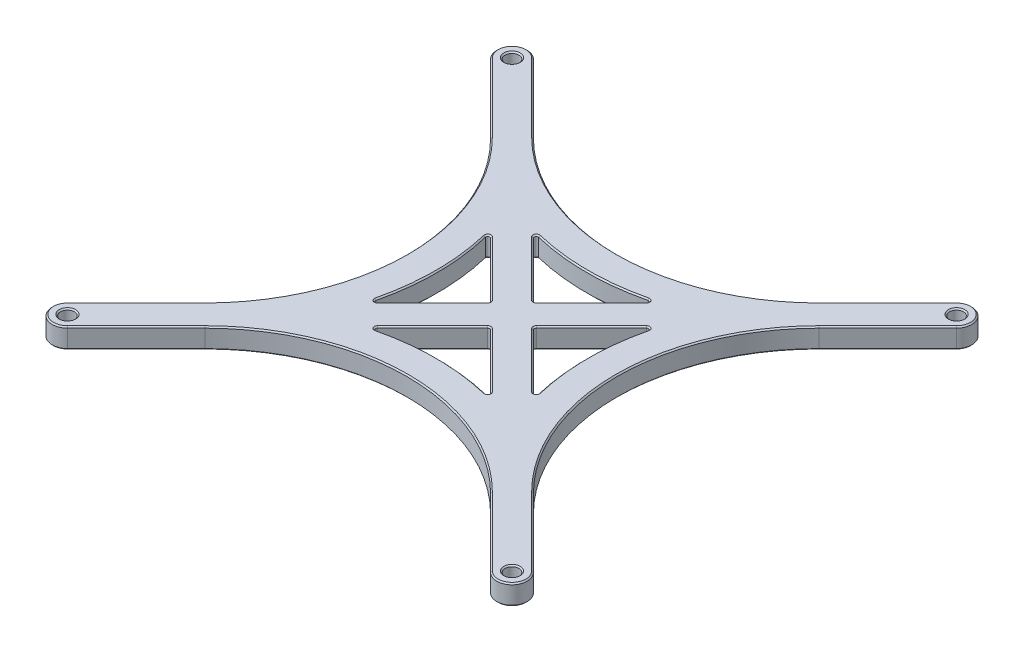
SolidWorks part; units mm, degrees
ref_plane "Front Plane" through (0, 0, 0) normal (0, 0, 1) x (1, 0, 0)
ref_plane "Top Plane" through (0, 0, 0) normal (0, 1, 0) x (1, 0, 0)
ref_plane "Right Plane" through (0, 0, 0) normal (1, 0, 0) x (0, 0, -1)
sketch "Sketch1" plane through (0, 0, 0) normal (0, 1, 0) x (1, 0, 0)
  line L0 (45.3593, 52.0945) -> (62.6658, 69.401)
  line L3 (-3.3676, 3.3676) -> (18.2135, 24.9487)
  line L18 (3.3676, -3.3676) -> (24.9487, 18.2135)
  line L19 (94.3407, 87.6055) -> (77.0342, 70.299)
  line L20 (3.3676, 143.0676) -> (24.9487, 121.4865)
  line L21 (-3.3676, 136.3324) -> (18.2135, 114.7513)
  line L22 (121.4865, 24.9487) -> (143.0676, 3.3676)
  line L23 (121.4865, 114.7513) -> (143.0676, 136.3324)
  line L24 (87.6055, 45.3593) -> (70.299, 62.6658)
  line L25 (52.0945, 94.3407) -> (69.401, 77.0342)
  line L26 (114.7513, 18.2135) -> (136.3324, -3.3676)
  line L27 (114.7513, 121.4865) -> (136.3324, 143.0676)
  line L28 (77.0342, 69.401) -> (94.3407, 52.0945)
  line L29 (62.6658, 70.299) -> (45.3593, 87.6055)
  line L30 (70.299, 77.0342) -> (87.6055, 94.3407)
  line L31 (69.401, 62.6658) -> (52.0945, 45.3593)
  circle A63 centre (0, 139.7) radius 2.1828
  circle A64 centre (0, 0) radius 2.1828
  circle A65 centre (139.7, 0) radius 2.1828
  circle A66 centre (139.7, 139.7) radius 2.1828
  arc A74 (-3.3676, 3.3676) -> (3.3676, -3.3676) centre (0, 0) ccw
  arc A75 (143.0676, 136.3324) -> (136.3324, 143.0676) centre (139.7, 139.7) ccw
  arc A76 (3.3676, 143.0676) -> (-3.3676, 136.3324) centre (0, 139.7) ccw
  arc A77 (136.3324, -3.3676) -> (143.0676, 3.3676) centre (139.7, 0) ccw
  arc A78 (18.2135, 114.7513) -> (18.2135, 24.9487) centre (-26.6878, 69.85) cw
  arc A79 (24.9487, 121.4865) -> (114.7513, 121.4865) centre (69.85, 166.3878) ccw
  arc A80 (121.4865, 24.9487) -> (121.4865, 114.7513) centre (166.3878, 69.85) cw
  arc A81 (24.9487, 18.2135) -> (114.7513, 18.2135) centre (69.85, -26.6878) cw
  arc A83 (44.2931, 52.6927) -> (44.2931, 87.0073) centre (-26.6878, 69.85) ccw
  arc A84 (52.6927, 95.4069) -> (87.0073, 95.4069) centre (69.85, 166.3878) ccw
  arc A85 (95.4069, 87.0073) -> (95.4069, 52.6927) centre (166.3878, 69.85) ccw
  arc A86 (87.0073, 44.2931) -> (52.6927, 44.2931) centre (69.85, -26.6878) ccw
  arc A87 (95.4069, 87.0073) -> (94.3407, 87.6055) centre (94.7897, 87.1565) ccw
  arc A88 (94.3407, 52.0945) -> (95.4069, 52.6927) centre (94.7897, 52.5435) ccw
  arc A89 (77.0342, 69.401) -> (77.0342, 70.299) centre (77.4832, 69.85) cw
  arc A90 (87.6055, 94.3407) -> (87.0073, 95.4069) centre (87.1565, 94.7897) ccw
  arc A91 (52.6927, 95.4069) -> (52.0945, 94.3407) centre (52.5435, 94.7897) ccw
  arc A92 (70.299, 77.0342) -> (69.401, 77.0342) centre (69.85, 77.4832) cw
  arc A93 (62.6658, 70.299) -> (62.6658, 69.401) centre (62.2168, 69.85) cw
  arc A94 (45.3593, 87.6055) -> (44.2931, 87.0073) centre (44.9103, 87.1565) ccw
  arc A95 (44.2931, 52.6927) -> (45.3593, 52.0945) centre (44.9103, 52.5435) ccw
  arc A96 (87.0073, 44.2931) -> (87.6055, 45.3593) centre (87.1565, 44.9103) ccw
  arc A97 (69.401, 62.6658) -> (70.299, 62.6658) centre (69.85, 62.2168) cw
  arc A98 (52.6927, 44.2931) -> (52.0945, 45.3593) centre (52.5435, 44.9103) cw
  point P1 (69.85, 69.85)
  point P9 (69.85, 69.85)
  point P23 (69.85, 76.5852)
  point P26 (76.5852, 69.85)
  point P29 (69.85, 63.1148)
  point P54 (69.85, 76.5852)
  point P65 (69.85, 63.1148)
  dimension "D5" = 4.7625
  dimension "D6" = 63.5
  dimension "D7" = 0.635
  dimension "D14" = 4.3656
  dimension "D16" = 4.3656
  dimension "D18" = 4.3656
  dimension "D19" = 4.3656
  dimension "D4" = 4.7625
  dimension "D2" = 139.7
  dimension "D3" = 139.7
extrude "Boss-Extrude1" add sketch "Sketch1" along normal blind 6.35
chamfer "Chamfer1" distance 0.3969 angle 45 88 edges at (44.5996, 0, -51.9897) (44.5996, 0, -87.7103) (62.8518, 0, -69.85) (-3.3676, 0, 3.3676) (143.0676, 0, 3.3676) (143.0676, 0, -143.0676) (-3.3676, 0, -143.0676) (69.85, 0, -36.8122) (95.1004, 0, -51.9897) (95.1004, 0, -87.7103) (0, 0, -137.5172) (0, 0, 2.1828) (139.7, 0, 2.1828) (139.7, 0, -137.5172) (87.7103, 0, -95.1004) (87.7103, 0, -44.5996) (69.85, 0, -62.8518) (62.8518, 6.35, -69.85) (44.5996, 6.35, -87.7103) (44.5996, 6.35, -51.9897) (-3.3676, 6.35, -143.0676) (143.0676, 6.35, -143.0676) (143.0676, 6.35, 3.3676) (-3.3676, 6.35, 3.3676) (69.85, 6.35, -36.8122) (95.1004, 6.35, -87.7103) (95.1004, 6.35, -51.9897) (0, 6.35, -137.5172) (0, 6.35, 2.1828) (139.7, 6.35, 2.1828) (139.7, 6.35, -137.5172) (87.7103, 6.35, -95.1004) (69.85, 6.35, -62.8518) (87.7103, 6.35, -44.5996) (51.9897, 0, -44.5996) (60.7477, 0, -54.0126) (78.9523, 0, -54.0126) (69.85, 0, -46.3372) (69.85, 0, -76.8482) (60.7477, 0, -85.6874) (51.9897, 0, -95.1004) (69.85, 0, -93.3628) (78.9523, 0, -85.6874) (76.8482, 0, -69.85) (85.6874, 0, -78.9523) (93.3628, 0, -69.85) (85.6874, 0, -60.7477) (125.5418, 0, -7.423) (132.277, 0, -14.1582) (102.8878, 0, -69.85) (132.277, 0, -125.5418) (125.5418, 0, -132.277) (69.85, 0, -102.8878) (14.1582, 0, -132.277) (7.423, 0, -125.5418) (36.8122, 0, -69.85) (7.423, 0, -14.1582) (14.1582, 0, -7.423) (46.3372, 0, -69.85) (54.0126, 0, -78.9523) (54.0126, 0, -60.7477) (78.9523, 6.35, -54.0126) (60.7477, 6.35, -54.0126) (51.9897, 6.35, -44.5996) (69.85, 6.35, -46.3372) (69.85, 6.35, -93.3628) (51.9897, 6.35, -95.1004) (60.7477, 6.35, -85.6874) (69.85, 6.35, -76.8482) (78.9523, 6.35, -85.6874) (93.3628, 6.35, -69.85) (85.6874, 6.35, -78.9523) (76.8482, 6.35, -69.85) (85.6874, 6.35, -60.7477) (7.423, 6.35, -14.1582) (36.8122, 6.35, -69.85) (7.423, 6.35, -125.5418) (14.1582, 6.35, -132.277) (69.85, 6.35, -102.8878) (125.5418, 6.35, -132.277) (132.277, 6.35, -125.5418) (102.8878, 6.35, -69.85) (132.277, 6.35, -14.1582) (125.5418, 6.35, -7.423) (14.1582, 6.35, -7.423) (54.0126, 6.35, -60.7477) (54.0126, 6.35, -78.9523) (46.3372, 6.35, -69.85)
